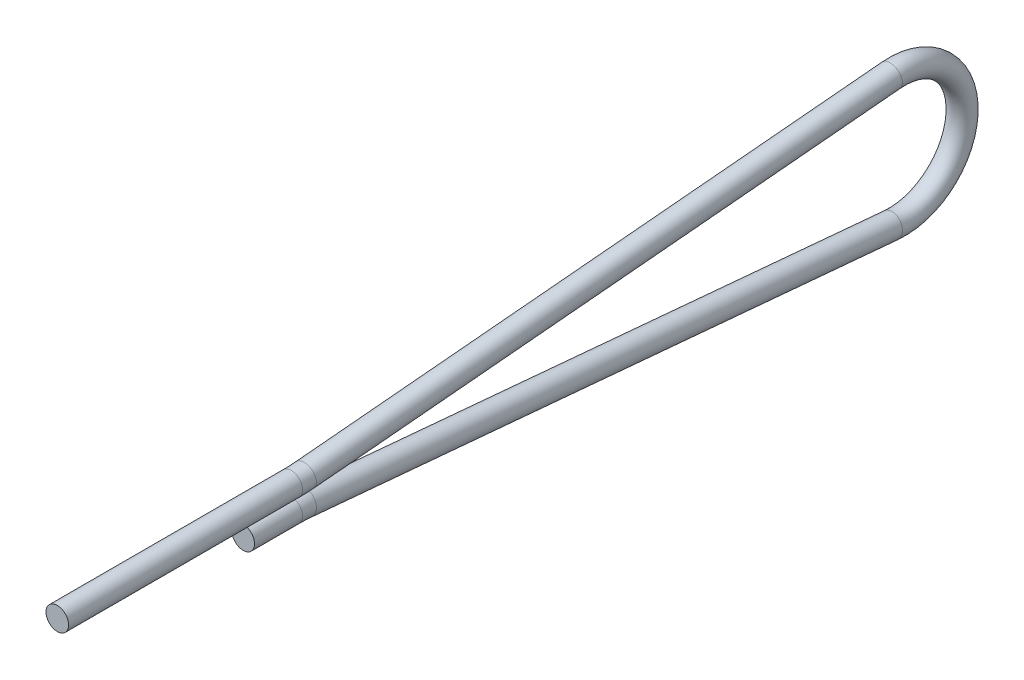
SolidWorks part; units mm, degrees
ref_plane "Front Plane" through (0, 0, 0) normal (0, 0, 1) x (1, 0, 0)
ref_plane "Top Plane" through (0, 0, 0) normal (0, 1, 0) x (1, 0, 0)
ref_plane "Right Plane" through (0, 0, 0) normal (1, 0, 0) x (0, 0, -1)
sketch "Sketch1" plane through (0, 0, 0) normal (1, 0, 0) x (0, 0, -1)
  line L0 (0, 0) -> (-38.9132, 0) construction
  line L1 (-39.3643, 0.7366) -> (-42.4838, 0.7366)
  line L2 (-39.3643, -0.7366) -> (-42.4838, -0.7366)
  line L3 (-42.4838, 0.7366) -> (-54.5646, 0.7366)
  line L4 (-38.9132, 13.9235) -> (-38.9132, -13.9235) construction
  line L5 (-38.4641, 0.7772) -> (-0.3814, 4.2194)
  line L6 (-38.4641, -0.7772) -> (-0.3814, -4.2194)
  arc A0 (-0.3814, -4.2194) -> (-0.3814, 4.2194) centre (0, 0) ccw
  arc A1 (-39.3643, -0.7366) -> (-38.4641, -0.7772) centre (-39.3643, -10.7366) cw
  arc A2 (-39.3643, 0.7366) -> (-38.4641, 0.7772) centre (-39.3643, 10.7366) ccw
  point P3 (-38.9132, 0)
  point P16 (-38.9132, -0.7366)
  point P19 (-38.9132, 0.7366)
  dimension "D1" = 8.4732
  dimension "D3" = 10
  dimension "D2" = 1.4732
ref_plane "Plane1" through (0, 0, 54.5646) normal (0, 0, 1) x (1, 0, 0)
sketch "Sketch2" plane through (0, 0, 54.5646) normal (0, 0, 1) x (1, 0, 0)
  circle A0 centre (0, 0.7366) radius 0.7366
  dimension "D1" = 1.4732
sweep "Sweep1" add profiles "Sketch2" path "Sketch1"
ref_plane "Plane2" through (0.7366, 0, 0) normal (1, 0, 0) x (0, 0, -1)
sketch "Sketch3" plane through (0.7366, 0, 0) normal (1, 0, 0) x (0, 0, -1)
  circle A0 centre (0, 0) radius 2.7304
